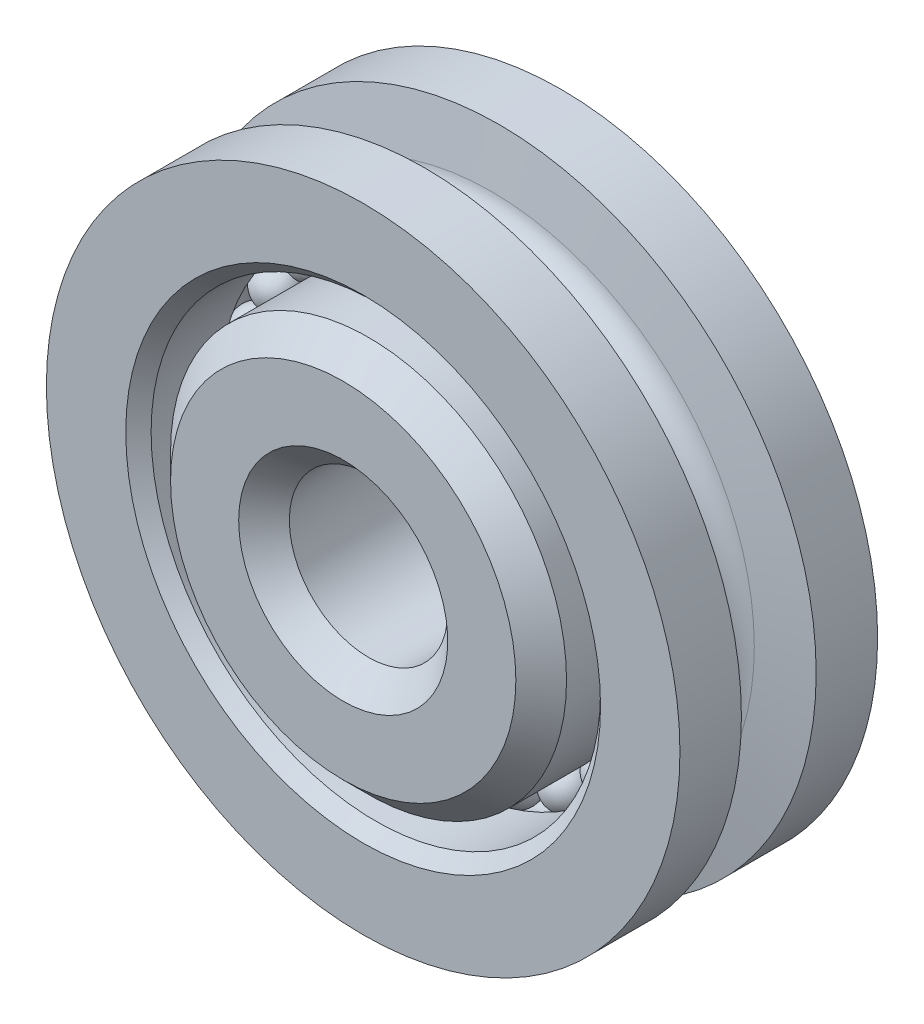
SolidWorks part; units mm, degrees
ref_plane "Front" through (0, 0, 0) normal (0, 0, 1) x (1, 0, 0)
ref_plane "Top" through (0, 0, 0) normal (0, 1, 0) x (1, 0, 0)
ref_plane "Right" through (0, 0, 0) normal (1, 0, 0) x (0, 0, -1)
sketch "Sketch1" plane through (0, 0, 0) normal (1, 0, 0) x (0, 0, -1)
  line L0 (0.7493, 6.35) -> (1.9812, 6.35)
  line L1 (-0.7493, 6.35) -> (-1.9812, 6.35)
  line L2 (-0.7493, 6.35) -> (-0.5888, 5.2703)
  line L3 (0.3572, 4.5045) -> (1.9812, 4.5045)
  line L4 (2.3812, 1.5875) -> (-2.3812, 1.5875)
  line L5 (-0.3572, 3.9688) -> (-2.3813, 3.9688)
  line L6 (0.7493, 6.35) -> (0.5888, 5.2703)
  line L8 (-2.3812, 0) -> (2.3812, 0) construction
  line L10 (1.9812, 6.35) -> (1.9812, 4.5045)
  line L13 (-2.3813, 3.9688) -> (-2.3812, 1.5875)
  line L14 (0, 4.7625) -> (0, -4.7625) construction
  line L16 (2.3813, 3.9688) -> (2.3812, 1.5875)
  line L17 (-1.9812, 6.35) -> (-1.9812, -6.35) construction
  line L18 (-1.9812, 4.5045) -> (-0.3572, 4.5045)
  line L20 (2.3813, 3.9688) -> (0.3572, 3.9688)
  line L21 (-1.9812, 4.5045) -> (-1.9812, 6.35)
  arc A0 (-0.5888, 5.2703) -> (0.5888, 5.2703) centre (0, 5.3578) ccw
  circle A1 centre (0, 5.3578) radius 0.5953 construction
  circle A2 centre (0, 0) radius 1.5875 construction
  circle A3 centre (0, 0) radius 3.9688 construction
  arc A4 (-0.3572, 3.9688) -> (0.3572, 3.9688) centre (0, 4.2366) ccw
  circle A5 centre (0, -5.3578) radius 0.5953 construction
  arc A6 (0.3572, 4.5045) -> (-0.3572, 4.5045) centre (0, 4.2366) ccw
  point P28 (-1.9812, 0)
  dimension "Rope Dia" = 1.1906
  dimension "Shaft Dia" = 3.175
  dimension "D1" = 7.9375
  dimension "D2" = 0.893
  dimension "Wd" = 4.7625
  dimension "D8" = 1.2319
  dimension "Groove Dia" = 9.525
  dimension "OD" = 12.7
  dimension "w Wd" = 3.9624
  dimension "D3" = 0.5358
revolve "Revolve1" add sketch "Sketch1" angle 360 about L8
sketch "Sketch2" plane through (0, 0, 0) normal (1, 0, 0) x (0, 0, -1)
  line L0 (0, 4.7625) -> (0, -4.7625) construction
  line L1 (0, 4.6831) -> (0, 3.7902)
  arc A0 (0.3572, 4.5045) -> (-0.3572, 4.5045) centre (0, 4.2366) ccw construction
  arc A1 (0, 3.7902) -> (0, 4.6831) centre (0, 4.2366) ccw
revolve "Revolve2" add sketch "Sketch2" angle 360 about L1
pattern_circular "CirPattern1" count 24 over 360 about axis through (0, 0, 0) along (0, 0, 1) of bodies 117
chamfer "Chamfer1" distance 0.508 angle 45 4 edges at (1.5875, 0, -2.3812) (3.9688, 0, -2.3813) (3.9688, 0, 2.3813) (1.5875, 0, 2.3812)
chamfer "Chamfer2" distance 0.254 angle 45 2 edges at (4.5045, 0, -1.9812) (4.5045, 0, 1.9812)
equation "\"D1@Sketch1\" = \"Shaft Dia@Sketch1\" * 2.5"
equation "\"D2@Sketch1\" = \"Rope Dia@Sketch1\" * .75"
equation "\"D3@Sketch1\" = \"D2@Sketch1\" * .6"
